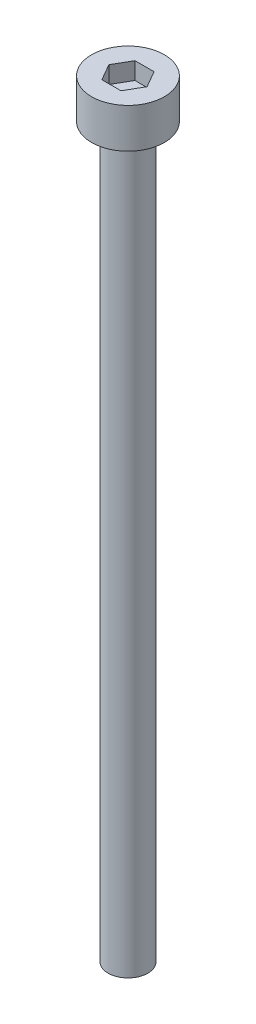
SolidWorks part; units mm, degrees
material "AISI 304"
ref_plane "前视基准面" through (0, 0, 0) normal (0, 0, 1) x (1, 0, 0)
ref_plane "上视基准面" through (0, 0, 0) normal (0, 1, 0) x (1, 0, 0)
ref_plane "右视基准面" through (0, 0, 0) normal (1, 0, 0) x (0, 0, -1)
sketch "草图1" plane through (0, 0, 0) normal (0, 1, 0) x (1, 0, 0)
  circle A0 centre (0, 0) radius 2.75
  dimension "D1" = 5.5
extrude "杯头" add sketch "草图1" along normal blind 3
sketch "草图2" plane through (0, 3, 0) normal (0, 1, 0) x (1, 0, 0)
  line L1 (1.4434, 0) -> (0.7217, 1.25)
  line L2 (0.7217, 1.25) -> (-0.7217, 1.25)
  line L3 (-0.7217, 1.25) -> (-1.4434, 0)
  line L4 (-1.4434, 0) -> (-0.7217, -1.25)
  line L5 (-0.7217, -1.25) -> (0.7217, -1.25)
  line L6 (0.7217, -1.25) -> (1.4434, 0)
  circle A0 centre (0, 0) radius 1.25 construction
  dimension "D1" = 2.5
extrude "内六角口" cut sketch "草图2" against normal blind 1.3
sketch "草图3" plane through (0, 0, 0) normal (0, -1, 0) x (1, 0, 0)
  circle A0 centre (0, 0) radius 1.5
  dimension "D1" = 3
extrude "螺纹长" add sketch "草图3" along normal blind 55
